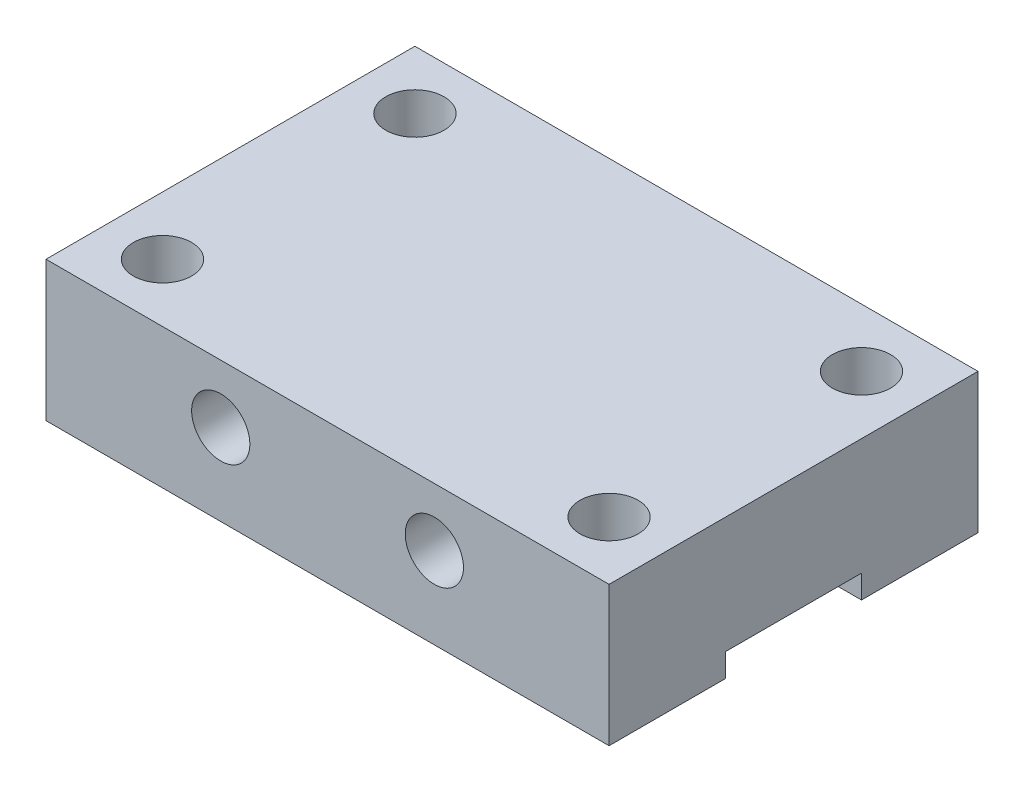
SolidWorks part; units mm, degrees
ref_plane "Front Plane" through (0, 0, 0) normal (0, 0, 1) x (1, 0, 0)
ref_plane "Top Plane" through (0, 0, 0) normal (0, 1, 0) x (1, 0, 0)
ref_plane "Right Plane" through (0, 0, 0) normal (1, 0, 0) x (0, 0, -1)
sketch "Sketch1" plane through (0, 0, 0) normal (0, 0, 1) x (1, 0, 0)
  line L5 (0, 0) -> (115, 0) construction
  line L6 (115, 0) -> (115, -32) construction
  line L7 (0, -32) -> (5, -32) construction
  line L8 (0, -32) -> (0, 0) construction
  line L9 (5, -32) -> (52.5, -32) construction
  line L10 (110, -32) -> (115, -32) construction
  line L11 (52.5, -32) -> (62.5, -32) construction
  line L12 (62.5, -32) -> (110, -32) construction
  line L13 (5, -32) -> (5, -6) construction
  line L14 (52.5, -32) -> (52.5, 0) construction
  line L15 (62.5, -32) -> (62.5, 0) construction
  line L16 (5, -6) -> (5, 0) construction
  line L17 (110, -32) -> (110, -6) construction
  line L18 (110, -6) -> (110, 0) construction
  line L19 (5, 0) -> (11, -6) construction
  line L20 (11, -6) -> (5, -6) construction
  line L21 (110, 0) -> (104, -6) construction
  line L22 (104, -6) -> (110, -6) construction
  line L23 (62.5, 0) -> (68.5, -6) construction
  line L24 (68.5, -6) -> (62.5, -6) construction
  line L25 (52.5, 0) -> (46.5, -6) construction
  line L26 (46.5, -6) -> (52.5, -6) construction
  point P22 (8, -3)
  point P23 (49.5, -3)
  point P24 (65.5, -3)
  point P25 (110, -3)
  dimension "D1" = 115
  dimension "D2" = 32
  dimension "D3" = 5
  dimension "D4" = 10
  dimension "D5" = 6
sketch "Sketch2" plane through (0, 0, 0) normal (0, 0, 1) x (1, 0, 0)
  line L0 (43, -6) -> (72, -6)
  line L1 (72, -6) -> (72, 0)
  line L2 (0, 0) -> (115, 0) construction
  line L4 (43, 0) -> (43, -6)
  line L5 (5, -6) -> (5, 0) construction
  line L6 (43, 0) -> (57.5, 0)
  line L7 (57.5, 0) -> (72, 0)
  dimension "D1" = 29
extrude "Boss-Extrude1" add sketch "Sketch2" along normal blind 19
sketch "Sketch3" plane through (0, -6, 0) normal (0, -1, 0) x (1, 0, 0)
  line L0 (57.5, 0) -> (57.5, 6) construction
  line L1 (0, 0) -> (115, 0) construction
  line L2 (57.5, 6) -> (57.5, 13) construction
  line L3 (57.5, 13) -> (57.5, 19) construction
  line L4 (43, 19) -> (72, 19) construction
  dimension "D1" = 7
ref_plane "Plane1" through (0, 0, 13) normal (0, 0, 1) x (1, 0, 0)
sketch "Sketch4" plane through (0, 0, 13) normal (0, 0, 1) x (1, 0, 0)
  line L0 (57.5, -5.2) -> (57.5, -6) construction
  line L1 (43, -6) -> (72, -6) construction
  line L2 (57.5, -6) -> (57.5, -6.8) construction
  line L3 (57.5, -6.8) -> (57.3, -6.8)
  line L4 (57.3, -6.8) -> (56.5, -5.2)
  line L5 (56.5, -5.2) -> (57.5, -5.2)
  line L6 (57.5, -5.2) -> (58.5, -5.2)
  line L7 (58.5, -5.2) -> (57.7, -6.8)
  line L8 (57.7, -6.8) -> (57.5, -6.8)
  dimension "D1" = 1.6
  dimension "D2" = 0.4
  dimension "D3" = 2
extrude "Boss-Extrude2" add sketch "Sketch4" against normal blind 7
pattern_linear "LPattern1" count 7 spacing 2 along (1, 0, 0) count 7 spacing 2 along (-1, 0, 0) of "Boss-Extrude2"
sketch "Sketch8" plane through (0, 0, 19) normal (0, 0, 1) x (1, 0, 0)
  line L1 (57.5, 0) -> (57.5, -6) construction
  line L2 (72, 0) -> (43, 0) construction
  line L3 (43, -6) -> (72, -6) construction
  line L4 (57.5, -3) -> (52, -3) construction
  line L5 (57.5, -3) -> (63, -3) construction
  circle A0 centre (52, -3) radius 1.5
  circle A1 centre (63, -3) radius 1.5
  dimension "D1" = 3
  dimension "D2" = 5.5
extrude "Cut-Extrude1" cut sketch "Sketch8" against normal up to surface (19 mm away) up to face at (57.5, -3, 0)
sketch "Sketch11" plane through (0, -6, 0) normal (0, -1, 0) x (1, 0, 0)
  line L0 (43, 19) -> (43, 13)
  line L1 (43, 19) -> (43, 0) construction
  line L2 (43, 13) -> (72, 13)
  line L3 (72, 19) -> (72, 0) construction
  line L4 (72, 13) -> (72, 19)
  line L5 (72, 19) -> (43, 19)
  line L6 (43, 0) -> (72, 0)
  line L7 (72, 0) -> (72, 6)
  line L8 (72, 6) -> (43, 6)
  line L9 (43, 6) -> (43, 0)
  line L10 (43, 13) -> (43, 6) construction
  dimension "D1" = 7
extrude "Boss-Extrude3" add sketch "Sketch11" along normal blind 1.2
sketch "Sketch9" plane through (0, -7.2, 0) normal (0, -1, 0) x (1, 0, 0)
  line L0 (43, 0) -> (49, 0) construction
  line L1 (0, 0) -> (115, 0) construction
  line L2 (49, 0) -> (43, 6) construction
  line L3 (43, 13) -> (43, 6) construction
  line L4 (43, 6) -> (43, 0) construction
  line L5 (43, 19) -> (49, 19) construction
  line L6 (43, 19) -> (72, 19) construction
  line L7 (49, 19) -> (43, 13) construction
  line L8 (43, 13) -> (43, 19) construction
  line L9 (72, 0) -> (66, 0) construction
  line L10 (66, 0) -> (72, 6) construction
  line L11 (72, 13) -> (72, 6) construction
  line L12 (72, 6) -> (72, 0) construction
  line L13 (72, 19) -> (72, 13) construction
  line L14 (72, 13) -> (66, 19) construction
  line L15 (66, 19) -> (72, 19) construction
  line L16 (72, 13) -> (72, 19) construction
  line L17 (43, 19) -> (43, 13) construction
  line L18 (72, 19) -> (43, 19) construction
  circle A0 centre (69, 16) radius 1.5
  circle A1 centre (69, 3) radius 1.5
  circle A2 centre (46, 3) radius 1.5
  circle A3 centre (46, 16) radius 1.5
  dimension "D2" = 3
  dimension "D1" = 6
extrude "Cut-Extrude2" cut sketch "Sketch9" against normal up to surface (7.2 mm away) up to face at (57.5, 0, 9.5)
equation "\"board_length\"= 260mm"
equation "\"board_height\"= 200mm"
equation "\"board_width\"= 16.5mm"
equation "\"token_thickness\"= 7mm"
equation "\"token_diameter\"= 32mm"
equation "\"board_side_lower_height\"= 55mm"
equation "\"board_side_height\"= 156.5mm"
equation "\"board_side_length\"= 100mm"
equation "\"board_slot_width\"= \"board_length\" / 7"
equation "\"token_ridge\"= ( \"token_thickness\" - 4mm ) / 2"
equation "\"token_ridge_width\"= 1.5mm"
equation "\"25T_outer_diameter\"= 20mm"
equation "\"25T_inner_diameter\"= 9mm"
equation "\"2T_screw_distance\" = 14mm"
equation "\"2T_outer_thickness\"= 2mm"
equation "\"2T_inner_thickness\"= 4.5mm"
equation "\"MG996R_outer_length\"= 54mm"
equation "\"MG996R_inner_length\"= 40mm"
equation "\"MG996R_width\"= 20mm"
equation "\"MG996R_height\" = 26.6mm"
equation "\"MG996R_full_height\"= 45.7mm"
equation "\"MG996R_full_width\"= 55.5mm"
equation "\"MG996R_screw_distance\"= 10mm"
equation "\"magnet_diameter\" = 10mm"
equation "\"magnet_thickness\"= 2mm"
equation "\"dispenser_barrel_margin\"= 2.5mm"
equation "\"dispenser_wheel_width\"= \"token_thickness\" + 5mm"
equation "\"dispenser_cover_margin\"= 3.0mm"
equation "\"dispenser_cover_thickness\"= 5.0mm"
equation "\"MG996R_major_axis_distance\"= 34.3mm"
equation "\"MG996R_major_screw_distance\"= 48.6mm"
equation "\"MG996R_minor_screw_distance\"= 9.9mm"
equation "\"MG996R_mid_height\"= 37.5mm"
equation "\"dispenser_slope\"= 30deg"
equation "\"dispenser_cover_length\"= 16mm"
equation "\"dispenser_carrier_width\" = 3.5mm"
equation "\"dispenser_carrier_height\"= 32mm"
equation "\"carrier_width\"= \"shaft_diameter\" * 2"
equation "\"shaft_diameter\"= 8mm"
equation "\"carrier_thickness\"=16"
equation "\"GT2_width\"= 7mm"
equation "\"GT2_outer_diameter\"= 18mm"
equation "\"GT2_inner_diameter\"= 12mm"
equation "\"GT2_pitch_diameter\"= 2mm"
equation "\"GT2_tooth_height\"= 1.6mm"
equation "\"GT2_upper_length\"= 0.4mm"
equation "\"D1@Sketch1\"=\"MG996R_outer_length\"*2+\"dispenser_cover_margin\"+4mm"
equation "\"D2@Sketch1\"=\"dispenser_carrier_height\""
equation "\"D3@Sketch1\"=\"dispenser_cover_thickness\""
equation "\"D4@Sketch1\"=\"dispenser_cover_thickness\"*2"
equation "\"belt_holder_width\"= \"GT2_width\" + 2 * 6mm"
equation "\"D1@Boss-Extrude1\"=\"belt_holder_width\""
equation "\"D1@Sketch3\"=\"GT2_width\""
equation "\"D1@Sketch4\"=\"GT2_tooth_height\""
equation "\"D2@Sketch4\"=\"GT2_upper_length\""
equation "\"D3@Sketch4\"=\"GT2_pitch_diameter\""
equation "\"D1@Boss-Extrude2\"=\"GT2_width\""
equation "\"D3@LPattern1\"=\"GT2_pitch_diameter\""
equation "\"D5@LPattern1\"=\"GT2_pitch_diameter\""
equation "\"D4@LPattern1\"=\"GT2_pitch_diameter\""
equation "\"D1@Sketch2\"=\"dispenser_cover_thickness\"+6mm*4"
equation "\"D1@Sketch11\"=\"GT2_width\""
equation "\"D1@Boss-Extrude3\"=\"GT2_pitch_diameter\"*0.6"
equation "\"D2@Sketch8\"=\"dispenser_cover_thickness\"/2+3mm"
